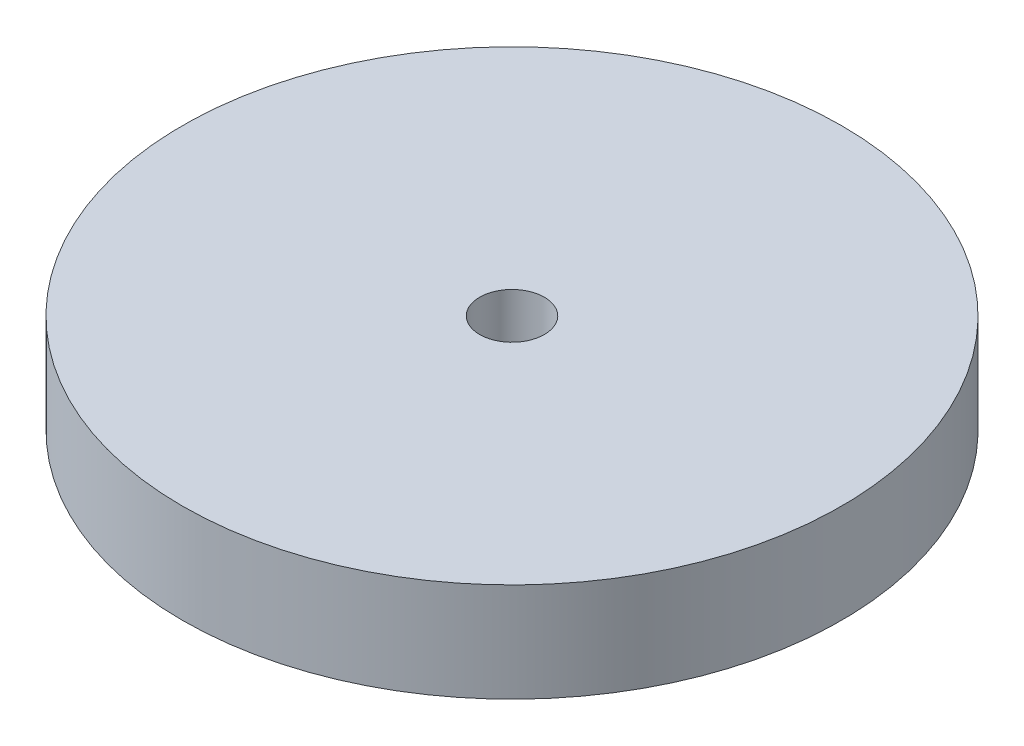
SolidWorks part; units mm, degrees
ref_plane "Front Plane" through (0, 0, 0) normal (0, 0, 1) x (1, 0, 0)
ref_plane "Top Plane" through (0, 0, 0) normal (0, 1, 0) x (1, 0, 0)
ref_plane "Right Plane" through (0, 0, 0) normal (1, 0, 0) x (0, 0, -1)
sketch "Sketch1" plane through (0, 0, 0) normal (0, 1, 0) x (1, 0, 0)
  circle A0 centre (0, 0) radius 25.3731
extrude "Boss-Extrude1" add sketch "Sketch1" along normal blind 7.62
sketch "Sketch2" plane through (0, 7.62, 0) normal (0, 1, 0) x (1, 0, 0)
  circle A0 centre (0, 0) radius 2.4923
  dimension "D1" = 4.9846
extrude "Cut-Extrude1" cut sketch "Sketch2" against normal blind 7.62
